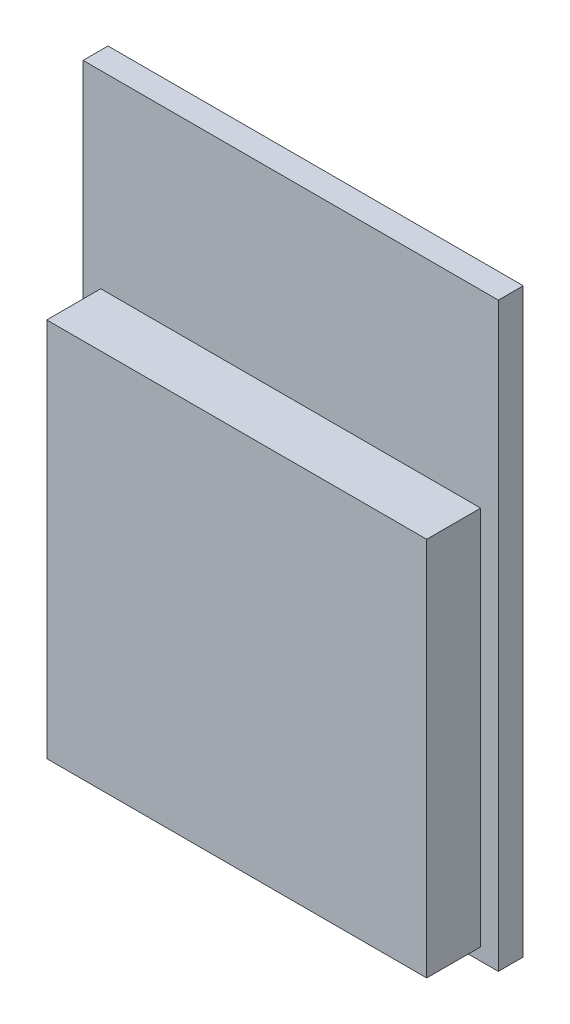
SolidWorks part; units mm, degrees
ref_plane "Front Plane" through (0, 0, 0) normal (0, 0, 1) x (1, 0, 0)
ref_plane "Top Plane" through (0, 0, 0) normal (0, 1, 0) x (1, 0, 0)
ref_plane "Right Plane" through (0, 0, 0) normal (1, 0, 0) x (0, 0, -1)
sketch "Sketch1" plane through (0, 0, 0) normal (0, 0, 1) x (1, 0, 0)
  line L1 (-5, -7) -> (5, -7)
  line L2 (-5, -7) -> (-5, 7)
  line L3 (-5, 7) -> (5, 7)
  line L4 (5, -7) -> (5, 7)
  line L5 (-5, -7) -> (5, 7) construction
  line L6 (-5, 7) -> (5, -7) construction
  point P0 (0, 0)
  dimension "D1" = 14
  dimension "D2" = 10
extrude "Boss-Extrude1" add sketch "Sketch1" along normal blind 0.6
sketch "Sketch2" plane through (0, 0, 0.6) normal (0, 0, 1) x (1, 0, 0)
  line L0 (0, 8.2194) -> (0, -10.3272) construction
  line L1 (-4.575, 2.45) -> (4.575, 2.45)
  line L2 (-4.575, 2.45) -> (-4.575, -6.7)
  line L3 (-4.575, -6.7) -> (4.575, -6.7)
  line L4 (4.575, 2.45) -> (4.575, -6.7)
  line L5 (-5, -7) -> (5, -7) construction
  point P7 (0, 2.45)
  dimension "D1" = 9.15
  dimension "D2" = 9.15
  dimension "D3" = 0.3
extrude "Boss-Extrude2" add sketch "Sketch2" along normal blind 1.3
